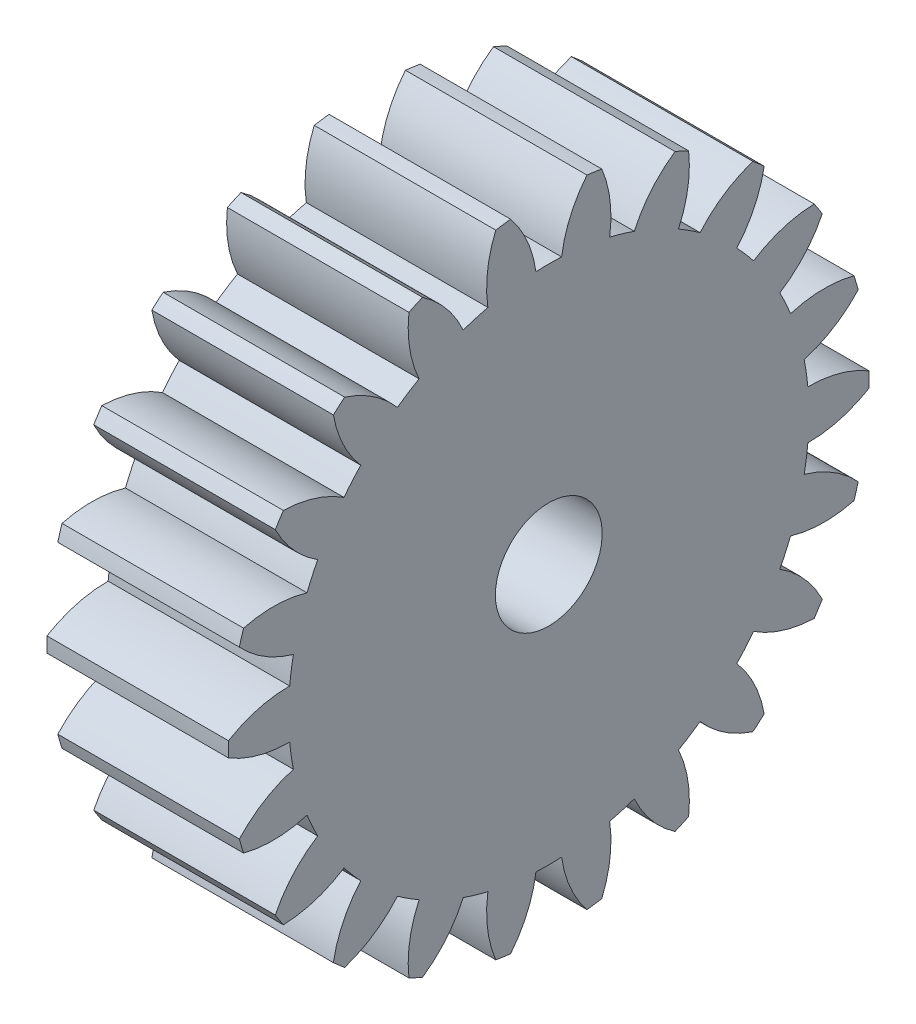
SolidWorks part; units mm, degrees
ref_plane "Plane1" through (0, 0, 0) normal (0, 0, 1) x (1, 0, 0)
ref_plane "Plane2" through (0, 0, 0) normal (0, 1, 0) x (1, 0, 0)
ref_plane "Plane3" through (0, 0, 0) normal (1, 0, 0) x (0, 0, -1)
sketch "HoldingSke" plane through (0, 0, 0) normal (0, 1, 0) x (1, 0, 0)
  line L0 (0, 0) -> (3.7087, -1.4984)
  line L1 (-15, 0) -> (100, 0) construction
  line L2 (0, 0) -> (-2.1039, 2.3779)
  line L3 (0, 0) -> (-11.863, 4.5341)
  line L4 (0, 0) -> (8.0072, 3.2351)
  line L5 (0, 0) -> (-46.8476, -17.4728)
  line L6 (0, 0) -> (-1.4092, -0.9508)
  line L7 (-2.1039, 2.3779) -> (8.6586, 51.2059)
  line L8 (-76.2, 54.61) -> (-76.1, 54.61)
  line L9 (-71.009, 38.7566) -> (-53.1078, 45.2721)
  line L10 (-76.2, 71.12) -> (104.1128, 71.12)
  line L11 (0, 0) -> (-1.7, 0)
  line L12 (-76.2, 101.6) -> (-76.192, 101.6)
  line L13 (24.9733, 27.94) -> (52.9518, 28.4284)
  line L14 (24.9733, 27.94) -> (24.9743, 27.94)
  line L15 (24.9733, 27.94) -> (100.4006, 29.5858)
  line L16 (-63.627, -0.25) -> (-12.827, -0.25)
  circle A0 centre (0, 0) radius 0.5
  circle A1 centre (0, 0) radius 2.4365
  circle A2 centre (0, 0) radius 37.5
  circle A3 centre (0, 0) radius 0.5
  dimension "MHD" = 4.873
  dimension "Hub_dia" = 75
  dimension "Bore" = 1
  dimension "MBD" = 1
  dimension "Num_teeth" = 22
  dimension "Pitch" = 4
  dimension "Overall_len" = 50
  dimension "Show_teeth" = 22
  dimension "Thickness" = 1.7
  dimension "OAL" = 50.0001
  dimension "T_dim" = 0.1
  dimension "Ap" = 20
  dimension "H" = 19.05
  dimension "Pitch_radius" = 180.3128
  dimension "Width" = 1.7
  dimension "Backlash" = 0.008
  dimension "Addendum_fac" = 1
  dimension "Dedendum_fac" = 1.25
  dimension "Clearance_fac" = 0.25
  dimension "Dedendum_add" = 0.001
  dimension "Module" = 0.25
sketch "BasProSke" plane through (0, 0, 0) normal (0, 1, 0) x (1, 0, 0)
  line L0 (-10, 0) -> (60, 0) construction
  line L1 (0, 0) -> (0, 3)
  line L2 (0, 0) -> (1.7, 0)
  line L3 (1.7, 0) -> (1.7, 3)
  line L4 (1.7, 3) -> (0, 3)
  dimension "Thickness" = 1.7
  dimension "Diameter" = 6
revolve "Base-Revolve" add sketch "BasProSke" angle 360 about L0
sketch "TooCutSke" plane through (0, 0, 0) normal (1, 0, 0) x (0, 0, -1)
  line L1 (0, 0) -> (0, 107) construction
  line L2 (0, 0) -> (-0.2102, 2.742) construction
  line L3 (0, 0) -> (-0.781, 5.4321) construction
  line L4 (-0.2102, 2.742) -> (-0.3905, 2.716) construction
  arc A0 (0.1203, 2.4335) -> (-0.1203, 2.4335) centre (0, 0) ccw
  arc A1 (0.3771, 3.0018) -> (-0.3771, 3.0018) centre (0, 0) ccw
  circle A2 centre (0, 0) radius 2.75 construction
  circle A3 centre (0, 0) radius 2.5842 construction
  arc A4 (-0.1203, 2.4335) -> (-0.3771, 3.0018) centre (-1.21, 2.2834) ccw
  arc A5 (0.3771, 3.0018) -> (0.1203, 2.4335) centre (1.21, 2.2834) ccw
  dimension "Root_dia" = 4.873
  dimension "Overcut_dia" = 6.0508
  dimension "Pitch_dia" = 5.5
  dimension "Base_dia" = 5.1683
  dimension "Flank_rad" = 1.1
  dimension "Half_ang" = 8.182
  dimension "Half_CT" = 0.1822
extrude "ToothCut" cut sketch "TooCutSke" along normal through all
fillet "Breaks" [suppressed] radius 0.005
fillet "RootFillets" [suppressed] radius 0.0635
pattern_circular "TeethCuts" count 22 every 16.364 about axis through (-10, 0, 0) along (1, 0, 0) of "ToothCut", "RootFillets", "Breaks"
sketch "HubNeaOneSke" plane through (0, 0, 0) normal (-1, 0, 0) x (0, 0, 1)
  circle A0 centre (0, 0) radius 2.4365
  dimension "Diameter" = 4.873
extrude "HubNearOne" [suppressed] add sketch "HubNeaOneSke" along normal blind 48.3001
sketch "HubNeaBotSke" plane through (0, 0, 0) normal (-1, 0, 0) x (0, 0, 1)
  circle A0 centre (0, 0) radius 2.4365
  dimension "Diameter" = 4.873
extrude "HubNearBoth" [suppressed] add sketch "HubNeaBotSke" along normal blind 24.15
ref_plane "FarPln" through (1.7, 0, 0) normal (1, 0, 0) x (0, 0, -1)
sketch "HubFarSke" plane through (1.7, 0, 0) normal (1, 0, 0) x (0, 0, -1)
  circle A0 centre (0, 0) radius 2.4365
  dimension "Diameter" = 4.873
extrude "HubFar" [suppressed] add sketch "HubFarSke" along normal blind 24.15
sketch "BorSke" plane through (0, 0, 0) normal (1, 0, 0) x (0, 0, -1)
  circle A0 centre (0, 0) radius 0.5
  dimension "Diameter" = 1
extrude "Bore" cut sketch "BorSke" along normal mid plane 100.0001
sketch "KeySke" plane through (0, 0, 0) normal (1, 0, 0) x (0, 0, -1)
  line L0 (-0.05, 0) -> (-0.05, 0.6)
  line L1 (-0.05, 0.6) -> (0.05, 0.6)
  line L2 (0.05, 0.6) -> (0.05, 0)
  line L3 (0, 0) -> (0, 34) construction
  line L4 (-0.05, 0) -> (0.05, 0)
  dimension "Offset" = 0.6
  dimension "Width" = 0.1
extrude "Keyway" [suppressed] cut sketch "KeySke" along normal mid plane 100.0001
pattern_circular "Keyway2" [suppressed] count 2 every 90 about axis through (-10, 0, 0) along (1, 0, 0)
equation "' \"Module@HoldingSke\" = 6.35"
equation "' \"Num_teeth@HoldingSke\" = 12"
equation "' \"Ap@HoldingSke\" =  20"
equation "' \"Ap@HoldingSke\" = 20"
equation "' \"Width@HoldingSke\" = 0.5 * 25.4"
equation "' \"Hub_dia@HoldingSke\"= 1 * 25.4"
equation "' \"Hub_dia@HoldingSke\" = 1 * 25.4"
equation "' \"Overall_len@HoldingSke\" = 1.0 * 25.4"
equation "' \"Bore@HoldingSke\" = 0.75 * 25.4"
equation "' \"T_dim@HoldingSke\" = 0.1 * 25.4"
equation "' \"Width@KeySke\" = 0.25 * 25.4"
equation "' \"Show_teeth@HoldingSke\" = 13"
equation "' \"Backlash@HoldingSke\" = 0.009 * 25.4"
equation "' \"Addendum_fac@HoldingSke\" = 1.0"
equation "' \"Dedendum_fac@HoldingSke\" = 1.25"
equation "' \"Dedendum_add@HoldingSke\" = 0.00005 * 25.4"
equation "' \"Clearance_fac@HoldingSke\" = 0.25"
equation "\"Pitch@HoldingSke\" = 1 / \"Module@HoldingSke\""
equation "\"Overcut_dia@TooCutSke\" = (\"Num_teeth@HoldingSke\" + 2 * \"Addendum_fac@HoldingSke\") / \"Pitch@HoldingSke\" + 0.002 * 25.4"
equation "\"Pitch_dia@TooCutSke\" = \"Num_teeth@HoldingSke\" / \"Pitch@HoldingSke\""
equation "\"Base_dia@TooCutSke\" = \"Num_teeth@HoldingSke\" / \"Pitch@HoldingSke\" * cos((\"Ap@HoldingSke\"  * 3.14159265 / 180))"
equation "\"Root_dia@TooCutSke\" = (\"Num_teeth@HoldingSke\" + 2) / \"Pitch@HoldingSke\" - 2 * (\"Addendum_fac@HoldingSke\" + \"Dedendum_fac@HoldingSke\") / \"Pitch@HoldingSke\" - \"Dedendum_add@HoldingSke\" * 2"
equation "\"Half_ang@TooCutSke\" = 180 / \"Num_teeth@HoldingSke\""
equation "\"Half_CT@TooCutSke\" = \"Num_teeth@HoldingSke\" / \"Pitch@HoldingSke\" * sin((3.14159265 / 2 / \"Num_teeth@HoldingSke\")) / 2 - 7 * \"Backlash@HoldingSke\" / 4"
equation "\"Flank_rad@TooCutSke\" = \"Num_teeth@HoldingSke\" / \"Pitch@HoldingSke\" / 5"
equation "\"Radius@RootFillets\" = \"Clearance_fac@HoldingSke\" / \"Pitch@HoldingSke\" + \"Dedendum_add@HoldingSke\""
equation "\"Break_rad@Breaks\" = 0.02 / \"Pitch@HoldingSke\""
equation "\"Thickness@HoldingSke\" = \"Width@HoldingSke\""
equation "\"OAL@HoldingSke\" = \"Thickness@HoldingSke\""
equation "\"MHD@HoldingSke\" = (\"Num_teeth@HoldingSke\" + 2) / \"Pitch@HoldingSke\" - 2 * (\"Addendum_fac@HoldingSke\" + \"Dedendum_fac@HoldingSke\")  / \"Pitch@HoldingSke\" - \"Dedendum_add@HoldingSke\" * 2"
equation "\"MBD@HoldingSke\" = (\"Num_teeth@HoldingSke\" + 2) / \"Pitch@HoldingSke\" - 2 * (\"Addendum_fac@HoldingSke\" + \"Dedendum_fac@HoldingSke\")  / \"Pitch@HoldingSke\" - \"Dedendum_add@HoldingSke\" * 2 - 0.002 * 25.4"
equation "\"MHD@HoldingSke\" = ((sgn( \"MHD@HoldingSke\" - \"Hub_dia@HoldingSke\" )-1)*( \"MHD@HoldingSke\" - \"Hub_dia@HoldingSke\" ))/-2+ \"Hub_dia@HoldingSke\""
equation "\"MBD@HoldingSke\" = ((sgn( \"MBD@HoldingSke\" - \"Bore@HoldingSke\" )-1)*( \"MBD@HoldingSke\" - \"Bore@HoldingSke\" ))/-2+ \"Bore@HoldingSke\""
equation "\"OAL@HoldingSke\" = ((sgn( \"OAL@HoldingSke\" - \"Overall_len@HoldingSke\" )+1)*( \"OAL@HoldingSke\" - \"Overall_len@HoldingSke\" ))/2 + \"Overall_len@HoldingSke\" + 0.000002 * 25.4"
equation "\"Num_teeth@TeethCuts\" = int( \"Show_teeth@HoldingSke\" ) + 1"
equation "\"Num_teeth@TeethCuts\" = ((sgn( \"Num_teeth@TeethCuts\" - \"Num_teeth@HoldingSke\" )-1)*( \"Num_teeth@TeethCuts\" - \"Num_teeth@HoldingSke\" ))/-2+ \"Num_teeth@HoldingSke\""
equation "\"Num_teeth@TeethCuts\" = ((sgn( \"Num_teeth@TeethCuts\" - 2.0)+1)*( \"Num_teeth@TeethCuts\" - 2.0))/2 +2.0"
equation "\"Angle@TeethCuts\" = 360.0 / \"Num_teeth@HoldingSke\""
equation "\"Diameter@BasProSke\" = (\"Num_teeth@HoldingSke\" + 2 * \"Addendum_fac@HoldingSke\") / \"Pitch@HoldingSke\""
equation "\"Thickness@BasProSke\"  = \"Thickness@HoldingSke\""
equation "' \"Fillet_rad@BasProSke\" =  \"Thickness@HoldingSke\" * 0.05"
equation "' \"Fillet_rad@BasProSke\" = \"Thickness@HoldingSke\" * 0.05"
equation "\"MHD@HoldingSke\" = ((sgn( \"MHD@HoldingSke\" - \"Root_dia@TooCutSke\" )-1)*( \"MHD@HoldingSke\" - \"Root_dia@TooCutSke\" ))/-2+ \"Root_dia@TooCutSke\""
equation "\"Diameter@HubNeaOneSke\" = \"MHD@HoldingSke\""
equation "\"Length@HubNearOne\" = \"OAL@HoldingSke\" - \"Thickness@BasProSke\""
equation "\"Diameter@HubNeaBotSke\" = \"MHD@HoldingSke\""
equation "\"Length@HubNearBoth\" = ( \"OAL@HoldingSke\" - \"Thickness@BasProSke\" ) / 2.0"
equation "\"Thickness@FarPln\" = \"Thickness@BasProSke\""
equation "\"Diameter@HubFarSke\" = \"MHD@HoldingSke\""
equation "\"Length@HubFar\" = ( \"OAL@HoldingSke\" - \"Thickness@BasProSke\" ) / 2.0"
equation "\"Diameter@BorSke\" = \"MBD@HoldingSke\""
equation "\"D1@Bore\" = \"OAL@HoldingSke\" * 2.0"
equation "\"D1@Keyway\" = \"OAL@HoldingSke\" * 2.0"
equation "\"Offset@KeySke\" = \"T_dim@HoldingSke\" + \"MBD@HoldingSke\" / 2.0"
